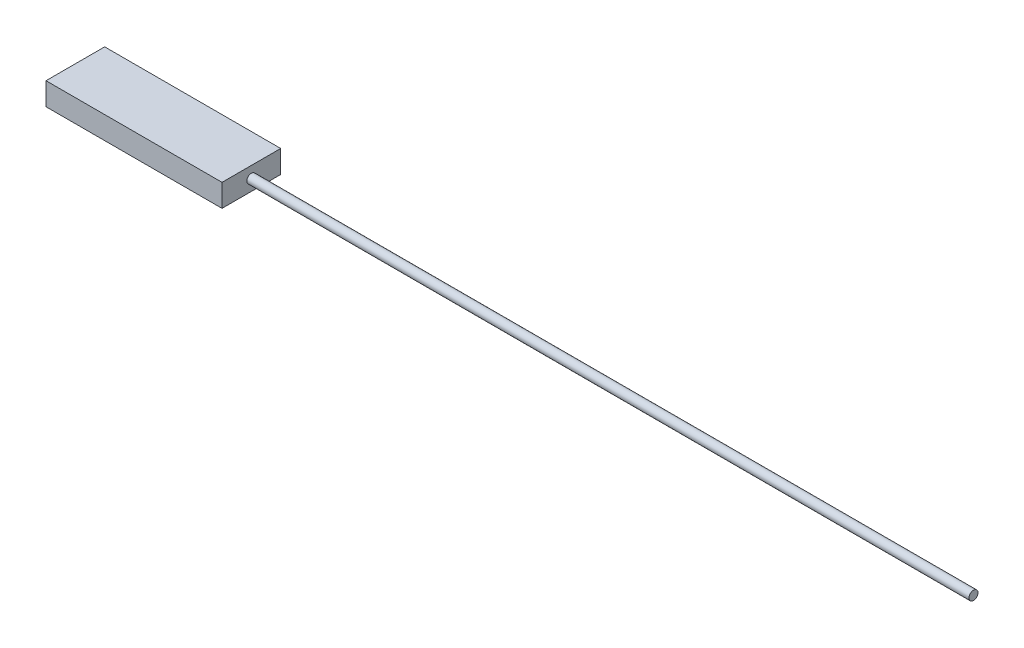
SolidWorks part; units mm, degrees
ref_plane "Front Plane" through (0, 0, 0) normal (0, 0, 1) x (1, 0, 0)
ref_plane "Top Plane" through (0, 0, 0) normal (0, 1, 0) x (1, 0, 0)
ref_plane "Right Plane" through (0, 0, 0) normal (1, 0, 0) x (0, 0, -1)
sketch "Sketch1" plane through (0, 0, 0) normal (0, 1, 0) x (1, 0, 0)
  line L1 (-49.53, -16.51) -> (49.53, -16.51)
  line L2 (-49.53, -16.51) -> (-49.53, 16.51)
  line L3 (-49.53, 16.51) -> (49.53, 16.51)
  line L4 (49.53, -16.51) -> (49.53, 16.51)
  line L5 (-49.53, -16.51) -> (49.53, 16.51) construction
  line L6 (-49.53, 16.51) -> (49.53, -16.51) construction
  point P0 (0, 0)
  dimension "D1" = 99.06
  dimension "D2" = 33.02
extrude "Boss-Extrude1" add sketch "Sketch1" along normal blind 12.7
sketch "Sketch2" plane through (49.53, 0, 0) normal (1, 0, 0) x (0, 0, -1)
  line L0 (0, 0) -> (0, 6.35) construction
  circle A0 centre (0, 6.35) radius 2.54
  dimension "D1" = 6.35
  dimension "D2" = 5.08
extrude "Boss-Extrude2" add sketch "Sketch2" along normal blind 406.4
